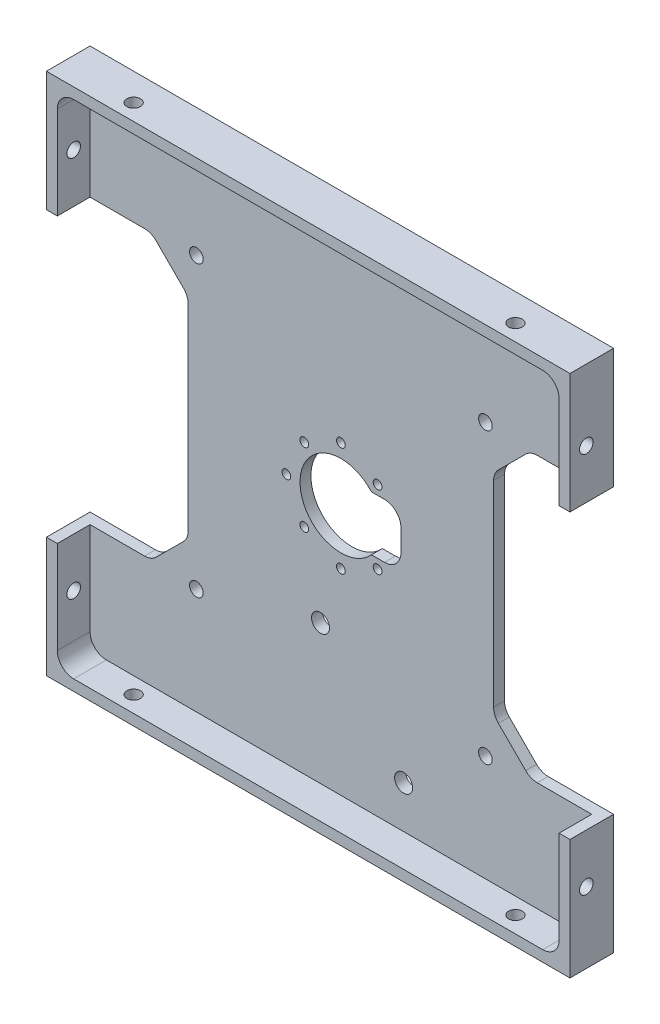
SolidWorks part; units mm, degrees
material "6061-T6 (SS)"
ref_plane "Front" through (0, 0, 0) normal (0, 0, 1) x (1, 0, 0)
ref_plane "Top" through (0, 0, 0) normal (0, 1, 0) x (1, 0, 0)
ref_plane "Right" through (0, 0, 0) normal (1, 0, 0) x (0, 0, -1)
sketch "Sketch1" plane through (0, 0, 0) normal (0, 0, 1) x (1, 0, 0)
  line L1 (-48, -48) -> (48, -48)
  line L2 (-48, -48) -> (-48, 48)
  line L3 (-48, 48) -> (48, 48)
  line L4 (48, -48) -> (48, 48)
  line L5 (-48, -48) -> (48, 48) construction
  line L6 (-48, 48) -> (48, -48) construction
  point P0 (0, 0)
  dimension "D1" = 96
  dimension "D2" = 96
extrude "Boss-Extrude1" add sketch "Sketch1" along normal blind 8
sketch "Sketch2" plane through (0, 0, 8) normal (0, 0, 1) x (1, 0, 0)
  line L1 (46, -46) -> (-46, -46)
  line L2 (46, -46) -> (46, 46)
  line L3 (46, 46) -> (-46, 46)
  line L4 (-46, -46) -> (-46, 46)
  line L5 (46, -46) -> (-46, 46) construction
  line L6 (46, 46) -> (-46, -46) construction
  point P0 (0, 0)
  dimension "D1" = 92
  dimension "D2" = 92
extrude "Component Platform" cut sketch "Sketch2" against normal blind 6
sketch "Sketch3" plane through (0, 0, 2) normal (0, 0, 1) x (1, 0, 0)
  line L1 (-33.8787, -25.1213) -> (-28.8787, -20.1213)
  line L2 (-33.8787, 25.1213) -> (-28.8787, 20.1213)
  line L3 (-28, -18) -> (-28, 18)
  line L4 (-48, -26) -> (-36, -26)
  line L7 (-48, 48) -> (-48, -48) construction
  line L8 (0, -56.7987) -> (0, 73.4321) construction
  line L9 (46, -46) -> (-57.8147, 57.8147) construction
  line L18 (46, 46) -> (-68.5705, -68.5705) construction
  line L23 (-48, 26) -> (-36, 26)
  line L26 (-48, -26) -> (-48, 26)
  line L28 (-48, -48) -> (48, -48) construction
  line L29 (48, -26) -> (48, 26)
  line L30 (48, 26) -> (36, 26)
  line L31 (33.8787, 25.1213) -> (28.8787, 20.1213)
  line L32 (28, -18) -> (28, 18)
  line L33 (33.8787, -25.1213) -> (28.8787, -20.1213)
  line L34 (48, -26) -> (36, -26)
  arc A3 (-28.8787, -20.1213) -> (-28, -18) centre (-31, -18) ccw
  arc A4 (-28.8787, 20.1213) -> (-28, 18) centre (-31, 18) cw
  arc A13 (-33.8787, -25.1213) -> (-36, -26) centre (-36, -23) cw
  arc A15 (-33.8787, 25.1213) -> (-36, 26) centre (-36, 23) ccw
  arc A17 (33.8787, 25.1213) -> (36, 26) centre (36, 23) cw
  arc A18 (28.8787, 20.1213) -> (28, 18) centre (31, 18) ccw
  arc A19 (28.8787, -20.1213) -> (28, -18) centre (31, -18) cw
  arc A20 (33.8787, -25.1213) -> (36, -26) centre (36, -23) ccw
  point P0 (-48, 0)
  point P37 (-48, 0)
  dimension "D2" = 3
  dimension "D3" = 3
  dimension "D4" = 20
  dimension "D6" = 3
  dimension "D7" = 3
  dimension "D8" = 135
  dimension "D5" = 52
  dimension "D9" = 135
  dimension "D10" = 12
  dimension "D11" = 12
  dimension "D12" = 48
extrude "Cable Slots" cut sketch "Sketch3" against normal mid plane 12
sketch "Sketch4" plane through (0, 0, 2) normal (0, 0, 1) x (1, 0, 0)
  circle A0 centre (0, 0) radius 7.5
  dimension "D1" = 15
extrude "Center Mass Cut" cut sketch "Sketch4" against normal blind 6
ref_plane "Center Y-Plane" through (0, 0, 0) normal (1, 0, 0) x (0, 0, -1)
ref_plane "Center X-Plane" through (0, 0, 0) normal (0, -1, 0) x (-1, 0, 0)
fillet "Inner Corner Fillets" radius 3 4 edges at (46, -46, 5) (-46, -46, 5) (46, 46, 5) (-46, 46, 5)
sketch "Sketch10" plane through (0, 0, 2) normal (0, 0, 1) x (1, 0, 0)
  line L1 (0, -5) -> (11, -5)
  line L2 (11, -5) -> (11, 5)
  line L3 (11, 5) -> (0, 5)
  line L5 (0, -5) -> (0, 5)
  point P3 (0, 0)
  dimension "D1" = 10
  dimension "D3" = 11
extrude "Motor Cutout" cut sketch "Sketch10" against normal blind 2
fillet "Fillet1" radius 3 2 edges at (11, 5, 1) (11, -5, 1)
sketch "Sketch11" plane through (0, 0, 2) normal (0, 0, 1) x (1, 0, 0)
  line L0 (0, 0) -> (0, 23.9217) construction
  line L1 (0, 0) -> (0, -24.7081) construction
  line L2 (0, 0) -> (-16.3847, 0) construction
  line L3 (0, 0) -> (16.7779, 0) construction
  circle A0 centre (6.72, 6.72) radius 1.05
  circle A1 centre (-6.72, 6.72) radius 1.05
  circle A2 centre (-6.72, -6.72) radius 1.05
  circle A3 centre (6.72, -6.72) radius 1.05
  circle A4 centre (0, 10) radius 1.05
  circle A5 centre (-10, 0) radius 1.05
  circle A6 centre (0, -10) radius 1.05
  dimension "D9" = 2.1
  dimension "D1" = 6.72
  dimension "D2" = 6.72
  dimension "D3" = 6.72
  dimension "D4" = 6.72
  dimension "D5" = 6.72
  dimension "D6" = 6.72
  dimension "D7" = 6.72
  dimension "D8" = 6.72
  dimension "D10" = 10
  dimension "D11" = 10
  dimension "D12" = 10
sketch "Sketch12" plane through (48, 0, 0) normal (1, 0, 0) x (0, 0, -1)
  line L0 (-5, -48) -> (-5, 48) construction
  line L1 (-8, -48) -> (0, -48) construction
  line L2 (-8, 48) -> (0, 48) construction
  line L3 (-8, -48) -> (-8, -26) construction
  dimension "D1" = 3
hole_wizard "M3x0.5 Tapped Hole1" positions "Sketch13" profile "Sketch14" tap size "M3x0.5" standard "ANSI Metric"
sketch "Sketch13" plane through (48, 0, 0) normal (1, 0, 0) x (0, 0, -1)
  line L0 (-5, -48) -> (-5, 48) construction
  point P0 (-5, -35)
  point P4 (-5, 35)
  dimension "D1" = 70
  dimension "D2" = 35
sketch "Sketch14" plane through (48, -35, 5) normal (0, 1, 0) x (0, 0, -1)
  line L0 (0, 0) -> (0, 8.2511)
  line L1 (0, 8.2511) -> (1.25, 7.5)
  line L2 (1.25, 7.5) -> (1.25, 0)
  line L5 (1.25, 0) -> (0, 0)
  line L10 (0, 8.2511) -> (-1.25, 7.5) construction
  line L11 (0, -6.35) -> (0, 107.95) construction
  dimension "Tap Drill Dia." = 2.5
  dimension "Tap Drill Depth" = 7.5
  dimension "Drill Angle" = 118
sketch "Sketch15" plane through (0, 48, 0) normal (0, 1, 0) x (1, 0, 0)
  line L0 (-48, -5) -> (48, -5) construction
  line L1 (-48, -8) -> (-48, 0) construction
  line L2 (48, -8) -> (48, 0) construction
  line L3 (48, -8) -> (-48, -8) construction
  dimension "D1" = 3
hole_wizard "M3x0.5 Tapped Hole2" positions "Sketch16" profile "Sketch17" tap size "M3x0.5" standard "ANSI Metric"
sketch "Sketch16" plane through (0, 48, 0) normal (0, 1, 0) x (1, 0, 0)
  line L0 (-48, -5) -> (48, -5) construction
  point P0 (35, -5)
  point P4 (-35, -5)
  dimension "D1" = 70
  dimension "D2" = 35
sketch "Sketch17" plane through (35, 48, 5) normal (1, 0, 0) x (0, 0, 1)
  line L0 (0, 0) -> (0, 8.2511)
  line L1 (0, 8.2511) -> (1.25, 7.5)
  line L2 (1.25, 7.5) -> (1.25, 0)
  line L5 (1.25, 0) -> (0, 0)
  line L10 (0, 8.2511) -> (-1.25, 7.5) construction
  line L11 (0, -6.35) -> (0, 107.95) construction
  dimension "Tap Drill Dia." = 2.5
  dimension "Tap Drill Depth" = 7.5
  dimension "Drill Angle" = 118
mirror "Mirror1" about plane through (0, 0, 0) normal (1, 0, 0) of "M3x0.5 Tapped Hole1"
mirror "Mirror2" about plane through (0, 0, 0) normal (0, -1, 0) of "M3x0.5 Tapped Hole2"
sketch "Sketch18" plane through (0, 0, 2) normal (0, 0, 1) x (1, 0, 0)
  line L0 (0, -46) -> (0, 46) construction
  line L1 (-43, -46) -> (43, -46) construction
  line L2 (43, 46) -> (-43, 46) construction
  line L6 (46, -28.5) -> (-46, -28.5) construction
  line L7 (46, -43) -> (46, -26) construction
  line L8 (-46, -26) -> (-46, -43) construction
  line L9 (-28.5, -46) -> (-28.5, 46) construction
  line L10 (-43, -46) -> (43, -46) construction
  dimension "D1" = 17.5
  dimension "D2" = 28.5
hole_wizard "M3x0.5 Tapped Hole3" positions "Sketch19" profile "Sketch20" tap size "M3x0.5" standard "ANSI Metric"
sketch "Sketch19" plane through (0, 0, 2) normal (0, 0, 1) x (1, 0, 0)
  line L20 (-43, -46) -> (43, -46) construction
  line L21 (-46, -26) -> (-46, -43) construction
  line L26 (43, 46) -> (-43, 46) construction
  line L27 (46, 26) -> (46, 43) construction
  line L28 (46, -43) -> (46, -26) construction
  line L29 (-46, 43) -> (-46, 26) construction
  point P49 (-26.5, -26.5)
  point P56 (-26.5, -26.5)
  point P67 (26.5, -26.5)
  point P70 (26.5, 26.5)
  point P73 (-26.5, 26.5)
  point P83 (26.5, -26.5)
  point P85 (26.5, 26.5)
  point P87 (-26.5, 26.5)
  dimension "D1" = 19.5
  dimension "D2" = 19.5
  dimension "D3" = 19.5
  dimension "D4" = 19.5
  dimension "D5" = 19.5
  dimension "D6" = 19.5
  dimension "D7" = 19.5
  dimension "D8" = 19.5
sketch "Sketch20" plane through (-26.5, -26.5, 2) normal (1, 0, 0) x (0, -1, 0)
  line L0 (0, 0) -> (0, 8.2511)
  line L1 (0, 8.2511) -> (1.25, 7.5)
  line L2 (1.25, 7.5) -> (1.25, 0)
  line L5 (1.25, 0) -> (0, 0)
  line L10 (0, 8.2511) -> (-1.25, 7.5) construction
  line L11 (0, -6.35) -> (0, 107.95) construction
  dimension "Tap Drill Dia." = 2.5
  dimension "Tap Drill Depth" = 7.5
  dimension "Drill Angle" = 118
cosmetic thread "Hole Thread1" parameters "D1"=2, "D2"=3
cosmetic thread "Hole Thread9" parameters "D1"=2, "D2"=3
cosmetic thread "Hole Thread10" parameters "D1"=2, "D2"=3
cosmetic thread "Hole Thread11" parameters "D1"=2, "D2"=3
hole_wizard "M2x0.4 Tapped Hole1" positions "Sketch23" profile "Sketch24" tap size "M2x0.4" standard "ANSI Metric"
sketch "Sketch23" plane through (0, 0, 2) normal (0, 0, 1) x (1, 0, 0)
  point P0 (6.72, -6.72)
  point P3 (0, -10)
  point P6 (-6.72, -6.72)
  point P9 (-10, 0)
  point P12 (-6.72, 6.72)
  point P15 (0, 10)
  point P18 (6.72, 6.72)
sketch "Sketch24" plane through (6.72, -6.72, 2) normal (1, 0, 0) x (0, -1, 0)
  line L0 (0, 0) -> (0, 5.6807)
  line L1 (0, 5.6807) -> (0.8, 5.2)
  line L2 (0.8, 5.2) -> (0.8, 0)
  line L5 (0.8, 0) -> (0, 0)
  line L10 (0, 5.6807) -> (-0.8, 5.2) construction
  line L11 (0, -6.35) -> (0, 107.95) construction
  dimension "Tap Drill Dia." = 1.6
  dimension "Tap Drill Depth" = 5.2
  dimension "Drill Angle" = 118
cosmetic thread "Hole Thread2" parameters "D1"=2, "D2"=2
cosmetic thread "Hole Thread3" parameters "D1"=2, "D2"=2
cosmetic thread "Hole Thread4" parameters "D1"=2, "D2"=2
cosmetic thread "Hole Thread5" parameters "D1"=2, "D2"=2
cosmetic thread "Hole Thread6" parameters "D1"=2, "D2"=2
cosmetic thread "Hole Thread7" parameters "D1"=2, "D2"=2
cosmetic thread "Hole Thread8" parameters "D1"=2, "D2"=2
sketch "Sketch25" plane through (0, 0, 2) normal (0, 0, 1) x (1, 0, 0)
  line L0 (0, -46) -> (0, 46) construction
  line L1 (-43, -46) -> (43, -46) construction
  line L2 (43, 46) -> (-43, 46) construction
  line L3 (-46, -38.25) -> (46, -38.25) construction
  line L4 (-46, -26) -> (-46, -43) construction
  line L5 (46, -43) -> (46, -26) construction
  line L6 (-43, -46) -> (43, -46) construction
  point P14 (11.5, -38.25)
  point P15 (-3.74, -20.47)
  dimension "D1" = 7.75
  dimension "D2" = 11.5
  dimension "D3" = 15.24
  dimension "D4" = 17.78
hole_wizard "M4x0.7 Tapped Hole1" positions "Sketch26" profile "Sketch27" tap size "M4x0.7" standard "ANSI Metric" end condition through all
sketch "Sketch26" plane through (0, 0, 2) normal (0, 0, 1) x (1, 0, 0)
  point P0 (-3.74, -20.47)
  point P3 (11.5, -38.25)
sketch "Sketch27" plane through (-3.74, -20.47, 2) normal (1, 0, 0) x (0, -1, 0)
  line L0 (0, 0) -> (0, 2)
  line L1 (0, 2) -> (1.65, 2)
  line L2 (1.65, 2) -> (1.65, 0)
  line L5 (1.65, 0) -> (0, 0)
  line L11 (0, -6.35) -> (0, 107.95) construction
  dimension "Thru Tap Drill Dia." = 3.3
  dimension "Thru Tap Drill Depth" = 2
cosmetic thread "Hole Thread12" parameters "D2"=4
cosmetic thread "Hole Thread13" parameters "D2"=4
